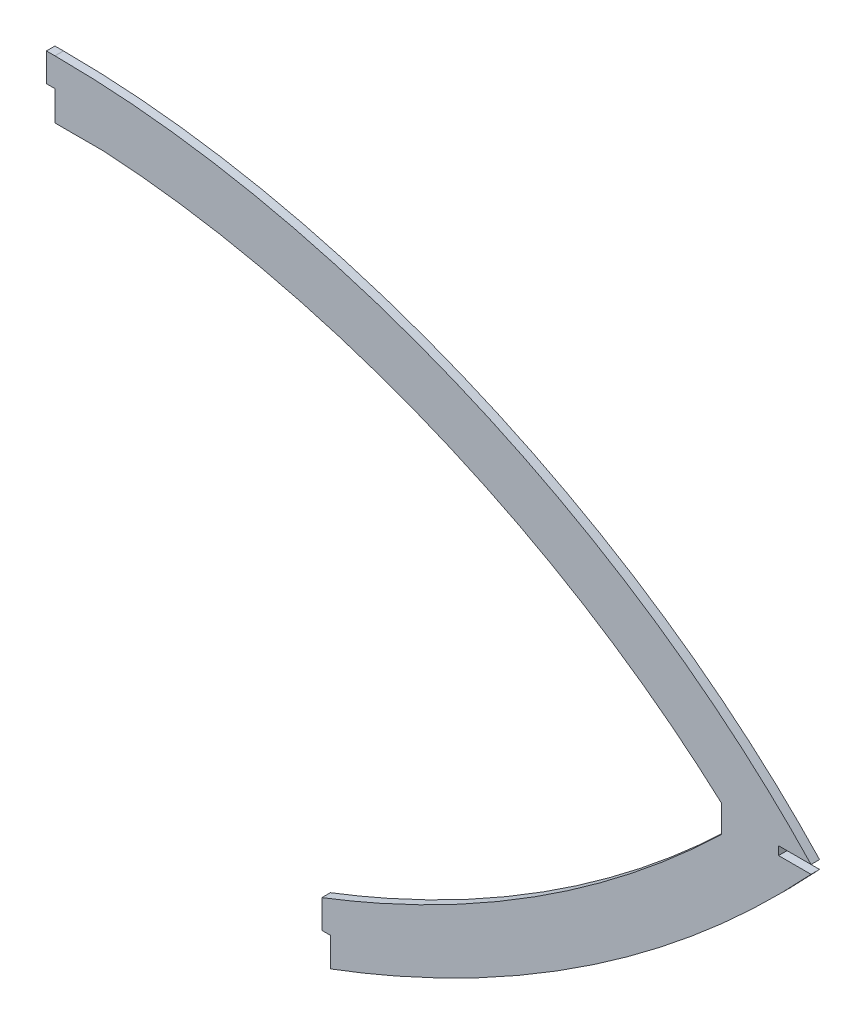
SolidWorks part; units mm, degrees
material "birch 3mm plywood"
ref_plane "Front" through (0, 0, 0) normal (0, 0, 1) x (1, 0, 0)
ref_plane "Top" through (0, 0, 0) normal (0, 1, 0) x (1, 0, 0)
ref_plane "Right" through (0, 0, 0) normal (1, 0, 0) x (0, 0, -1)
sketch "Sketch1" plane through (0, 0, 0) normal (0, 0, 1) x (1, 0, 0)
  line L2 (162, 160.5) -> (159, 160.5)
  line L3 (159, 160.5) -> (159, 150.5)
  line L4 (159, 150.5) -> (162, 150.5)
  line L5 (428.2878, 47) -> (416.8417, 47)
  line L6 (429.6834, 47) -> (162, 47) construction
  line L7 (416.8417, 47) -> (416.8417, 44)
  line L8 (416.8417, 44) -> (428.2966, 44)
  line L9 (162, 44) -> (429.6834, 44) construction
  line L10 (179.0354, 140.0216) -> (179.0354, 140.0216)
  line L11 (179.0354, 140.0216) -> (179.0354, 140.0216)
  line L12 (179.0354, 140.0216) -> (179.0354, 140.0216)
  line L13 (396.8417, 49.8799) -> (396.8417, 49.8799)
  line L14 (396.8417, 49.8799) -> (396.8417, 40.4728)
  line L15 (396.8417, 40.4728) -> (396.8417, 40.4728)
  line L16 (179.0354, 140.0216) -> (162, 140.0216)
  line L18 (162, 140.0216) -> (162, 150.5)
  line L19 (259, -69.5) -> (259, -59.2433)
  line L21 (259, -59.2433) -> (256, -59.2433)
  line L22 (256, -50.5) -> (256, -62.5) construction
  line L23 (256, -59.2433) -> (256, -49.2433)
  line L24 (256, -40.5) -> (256, -50.5) construction
  parabola Q1 (429.6834, 45.5) -> (259, -69.5) focus (230.0403, 156.4144) apex (350.0839, -22.9206) construction
  parabola Q2 (428.2966, 44) -> (259, -69.5) focus (230.0403, 156.4144) apex (350.0839, -22.9206)
  spline S0 degree 1 poles (179.0354, 140.0216) (396.8417, 49.8799) knots 0 0 1 1 construction
  spline S1 degree 3 poles (1744.7093, -2233.5771) (-3052.7667, 1873.6999) (3974.8607, -419.7047) (-2236.4182, -1019.2772) knots -3.570308 -3.570308 -3.570308 -3.570308 4.409177 4.409177 4.409177 4.409177 only from (162, 160.5) to (429.6834, 45.5) construction
  spline S2 degree 3 poles (162, 160.5) (257.4074, 160.5) (362.2697, 117.4672) (428.2878, 47) knots 0 0 0 0 0.992974 0.992974 0.992974 0.992974
  spline S3 degree 1 poles (396.8417, 40.4728) (251.9791, -50.7728) knots 0 0 1 1 construction
  spline S4 degree 3 poles (179.0354, 140.0216) (181.4518, 139.8872) (186.2712, 139.5636) (195.9767, 138.6926) (208.1599, 137.1905) (222.8333, 134.7367) (242.3999, 130.613) (266.7477, 123.8921) (295.4132, 113.4313) (323.1566, 100.6949) (345.203, 88.2923) (362.0163, 77.366) (374.171, 68.6867) (383.882, 61.0677) (391.3843, 54.7451) (395.0337, 51.5181) (396.8417, 49.8799) knots 0.062605 0.062605 0.062605 0.062605 0.088989 0.115372 0.168139 0.220906 0.273673 0.379207 0.484741 0.590275 0.695809 0.748576 0.801343 0.85411 0.880493 0.906877 0.906877 0.906877 0.906877
  spline S5 degree 3 poles (396.8417, 40.4728) (394.239, 37.9596) (388.9614, 32.9903) (378.2295, 23.3874) (364.4299, 11.9611) (347.2661, -0.8173) (329.4875, -12.6724) (311.0878, -23.6078) (292.0612, -33.6267) (275.6705, -41.2161) (262.2468, -46.8269) (255.4071, -49.4876) (251.9791, -50.7728) knots 0.498678 0.498678 0.498678 0.498678 0.498869 0.49906 0.499441 0.499822 0.500204 0.500585 0.500966 0.501348 0.501538 0.501729 0.501729 0.501729 0.501729 only from (396.8417, 40.4728) to (256, -49.2433)
  point P34 (0, 0)
  dimension "D1" = 20
  dimension "D2" = 10
extrude "Boss-Extrude1" add sketch "Sketch1" along normal mid plane 3 contours L16 L18 L4 L3 L2 S2 L5 L7 L8 Q2 L19 L21 L23 S5 L15 L14 L13 S4
